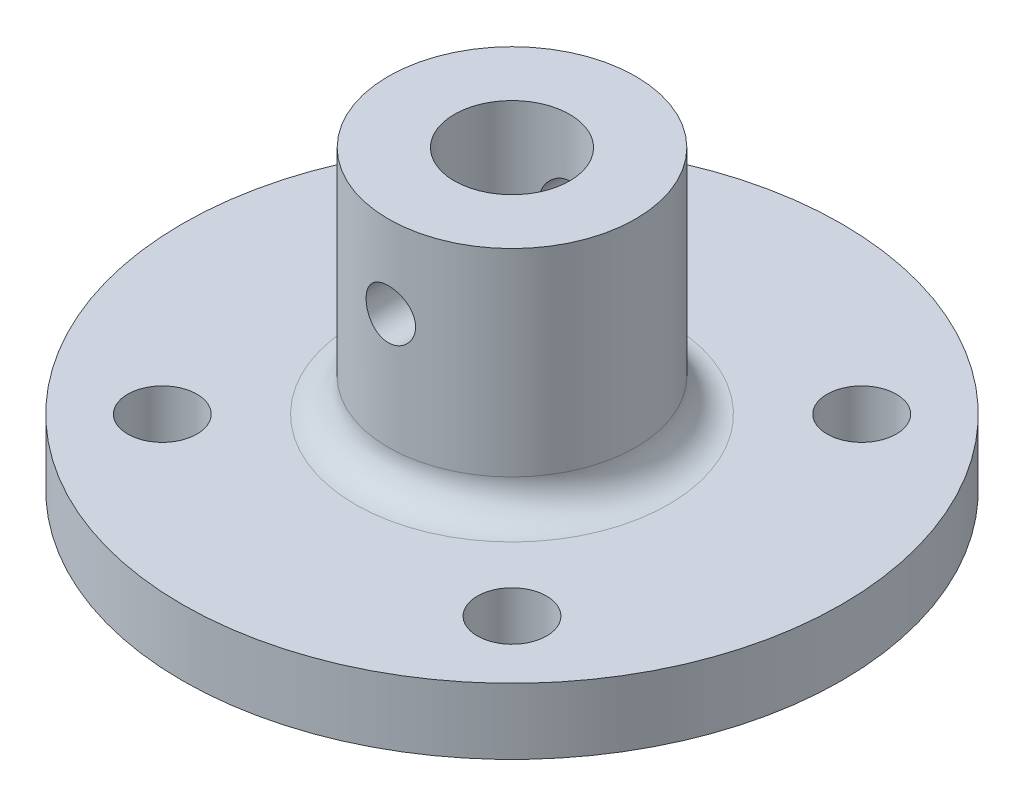
SolidWorks part; units mm, degrees
ref_plane "Front Plane" through (0, 0, 0) normal (0, 0, 1) x (1, 0, 0)
ref_plane "Top Plane" through (0, 0, 0) normal (0, 1, 0) x (1, 0, 0)
ref_plane "Right Plane" through (0, 0, 0) normal (1, 0, 0) x (0, 0, -1)
sketch "Sketch1" plane through (0, 0, 0) normal (0, 1, 0) x (1, 0, 0)
  circle A0 centre (0, 0) radius 20
extrude "Boss-Extrude1" add sketch "Sketch1" along normal blind 4
sketch "Sketch2" plane through (0, 4, 0) normal (0, 1, 0) x (1, 0, 0)
  circle A0 centre (0, 0) radius 7.5
extrude "Boss-Extrude2" add sketch "Sketch2" along normal blind 14
sketch "Sketch3" plane through (0, 18, 0) normal (0, 1, 0) x (1, 0, 0)
  circle A0 centre (0, 0) radius 3.5
extrude "Cut-Extrude1" cut sketch "Sketch3" against normal blind 14 contours A0
sketch "Sketch4" plane through (0, 0, 0) normal (0, 0, 1) x (1, 0, 0)
  line L0 (-7.5, 18) -> (-7.5, 4)
  line L1 (7.5, 18) -> (7.5, 4)
ref_plane "Plane1" through (0, 0, 0) normal (0, 0, 1) x (1, 0, 0)
sketch "Sketch5" plane through (0, 0, 0) normal (0, 0, 1) x (1, 0, 0)
  line L0 (0, 4) -> (0, 13) construction
  line L1 (20, 4) -> (-20, 4) construction
  circle A0 centre (0, 13) radius 1.5
  dimension "D2" = 3
  dimension "D1" = 9
extrude "Cut-Extrude2" cut sketch "Sketch5" against normal through all and the other way through all
fillet "Fillet1" radius 2 1 edges at (0, 4, 7.5)
sketch "Sketch6" plane through (0, 4, 0) normal (0, 1, 0) x (1, 0, 0)
  line L0 (10.6066, 10.6066) -> (10.6066, -10.6066) construction
  line L1 (10.6066, 10.6066) -> (-10.6066, 10.6066) construction
  line L2 (-10.6066, 10.6066) -> (-10.6066, -10.6066) construction
  circle A0 centre (0, 0) radius 15 construction
  circle A1 centre (10.6066, 10.6066) radius 2.1
  circle A3 centre (-10.6066, 10.6066) radius 2.1
  circle A4 centre (-10.6066, -10.6066) radius 2.1
  circle A5 centre (10.6066, -10.6066) radius 2.1
  dimension "D1" = 4.2
  dimension "D2" = 4.2
  dimension "D3" = 4.2
  dimension "D4" = 4.2
extrude "Cut-Extrude3" cut sketch "Sketch6" against normal through all
